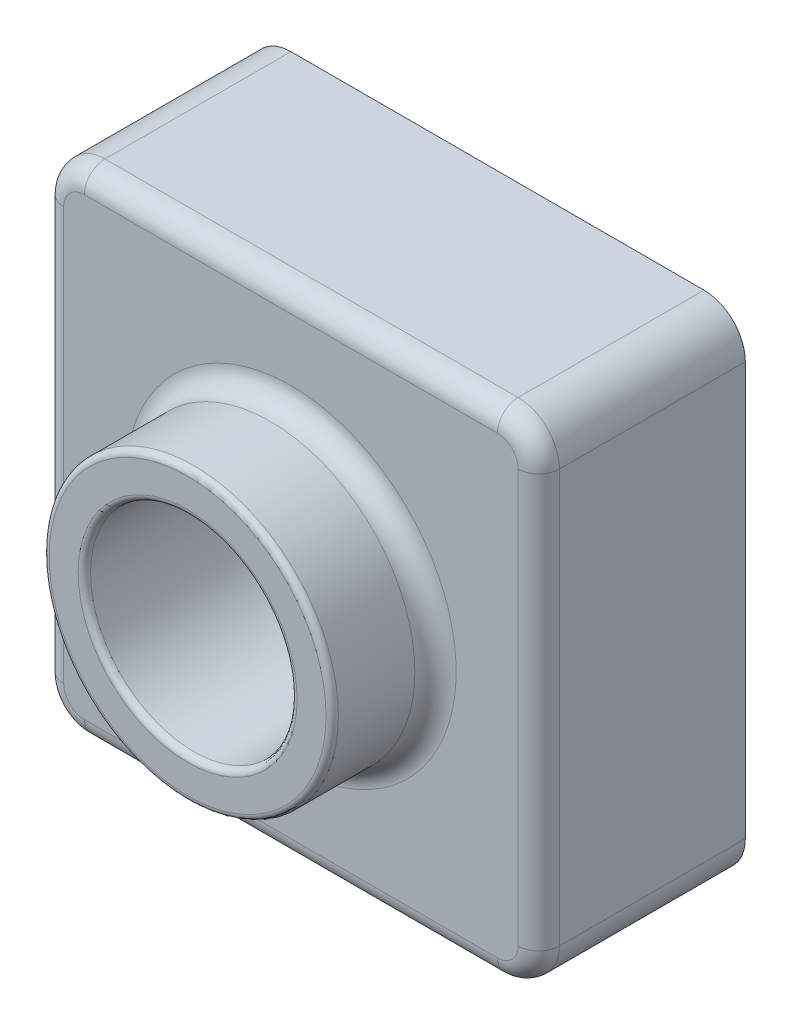
SolidWorks part; units mm, degrees
material "Copper"
ref_plane "Front Plane" through (0, 0, 0) normal (0, 0, 1) x (1, 0, 0)
ref_plane "Top Plane" through (0, 0, 0) normal (0, 1, 0) x (1, 0, 0)
ref_plane "Right Plane" through (0, 0, 0) normal (1, 0, 0) x (0, 0, -1)
sketch "Sketch1" plane through (0, 0, 0) normal (0, 0, 1) x (1, 0, 0)
  line L1 (0, 0) -> (120, 0)
  line L2 (0, 0) -> (0, 120)
  line L3 (0, 120) -> (120, 120)
  line L4 (120, 0) -> (120, 120)
  dimension "D1" = 120
  dimension "D2" = 120
extrude "Boss-Extrude1" add sketch "Sketch1" along normal blind 50
sketch "Sketch3" plane through (0, 0, 50) normal (0, 0, 1) x (1, 0, 0)
  line L0 (120, 120) -> (0, 120) construction
  line L1 (120, 0) -> (120, 120) construction
  circle A0 centre (60, 60) radius 35
  dimension "D1" = 70
  dimension "D2" = 60
  dimension "D3" = 60
extrude "Boss-Extrude2" add sketch "Sketch3" along normal blind 25
sketch "Sketch4" plane through (0, 0, 75) normal (0, 0, 1) x (1, 0, 0)
  circle A0 centre (60, 60) radius 25
  dimension "D1" = 50
extrude "Cut-Extrude1" cut sketch "Sketch4" against normal through all
fillet "Fillet1" radius 10 4 edges at (0, 0, 25) (120, 120, 25) (120, 0, 25) (0, 120, 25)
shell "Shell1" thickness 2
fillet "Fillet8" radius 1.5 2 edges at (85, 60, 75) (95, 60, 75)
fillet "Fillet9" radius 5 9 edges at (2.9289, 117.0711, 50) (60, 120, 50) (117.0711, 117.0711, 50) (120, 60, 50) (117.0711, 2.9289, 50) (60, 0, 50) (2.9289, 2.9289, 50) (0, 60, 50) (95, 60, 50)
